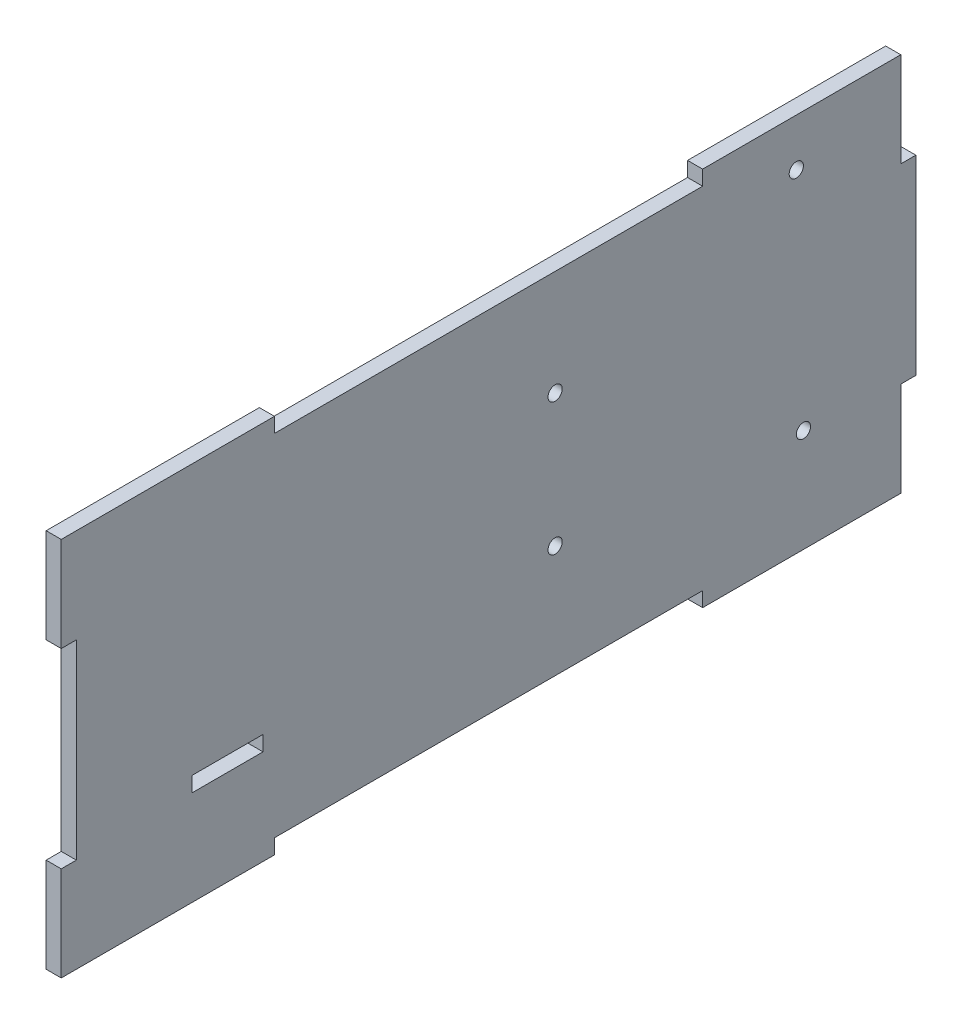
SolidWorks part; units mm, degrees
ref_plane "Front Plane" through (0, 0, 0) normal (0, 0, 1) x (1, 0, 0)
ref_plane "Top Plane" through (0, 0, 0) normal (0, 1, 0) x (1, 0, 0)
ref_plane "Right Plane" through (0, 0, 0) normal (1, 0, 0) x (0, 0, -1)
sketch "Sketch2" plane through (0, 0, 0) normal (1, 0, 0) x (0, 0, -1)
  line L1 (90, -40) -> (-90, -40)
  line L2 (90, -40) -> (90, 40)
  line L3 (90, 40) -> (-90, 40)
  line L4 (-90, -40) -> (-90, 40)
  line L5 (90, -40) -> (-90, 40) construction
  line L6 (90, 40) -> (-90, -40) construction
  point P0 (0, 0)
  dimension "D1" = 180
  dimension "D2" = 80
extrude "Boss-Extrude1" add sketch "Sketch2" along normal blind 3.18
sketch "Sketch3" plane through (3.18, 0, 0) normal (1, 0, 0) x (0, 0, -1)
  line L0 (-90, 40) -> (-90, -40) construction
  line L1 (-90, -20.09) -> (-86.82, -20.09)
  line L2 (-90, -20.09) -> (-90, 20.09)
  line L3 (-90, 20.09) -> (-86.82, 20.09)
  line L4 (-86.82, -20.09) -> (-86.82, 20.09)
  line L11 (0, 0) -> (-100.6733, 0) construction
  point P6 (-90, 0)
  dimension "D1" = 3.18
  dimension "D2" = 40.18
extrude "Cut-Extrude1" cut sketch "Sketch3" against normal up to surface (3.18 mm away) up to face at (0, 0, 0)
sketch "Sketch4" plane through (3.18, 0, 0) normal (1, 0, 0) x (0, 0, -1)
  line L0 (90, 40) -> (-90, 40) construction
  line L1 (-45.09, 40) -> (45.09, 40)
  line L2 (-45.09, 40) -> (-45.09, 36.88)
  line L3 (-45.09, 36.88) -> (45.09, 36.88)
  line L4 (45.09, 40) -> (45.09, 36.88)
  line L7 (0, 0) -> (0, 98.844) construction
  point P13 (0, 40)
  dimension "D1" = 3.12
  dimension "D2" = 90.18
extrude "Cut-Extrude2" cut sketch "Sketch4" against normal up to surface (3.18 mm away) up to face at (0, 0, 44.205)
mirror "Mirror1" about plane through (0, 0, 0) normal (0, 1, 0) of "Cut-Extrude2"
sketch "Sketch5" plane through (3.18, 0, 0) normal (1, 0, 0) x (0, 0, -1)
  line L1 (90, 40) -> (86.82, 40)
  line L2 (90, 40) -> (90, 20.09)
  line L3 (90, 20.09) -> (86.82, 20.09)
  line L4 (86.82, 40) -> (86.82, 20.09)
  line L5 (45.09, -40) -> (90, -40) construction
  dimension "D1" = 3.18
  dimension "D3" = 60.09
  dimension "D2" = 19.91
extrude "Cut-Extrude3" cut sketch "Sketch5" against normal up to surface (3.18 mm away) up to face at (0, 0, 22.1025)
mirror "Mirror2" about plane through (0, 0, 0) normal (0, 1, 0) of "Cut-Extrude3"
sketch "Sketch7" plane through (3.18, 0, 0) normal (1, 0, 0) x (0, 0, -1)
  line L0 (66.32, 30) -> (66.32, -16.8) construction
  line L1 (86.82, 20.09) -> (86.82, 40) construction
  line L2 (14.02, 14.7) -> (14.02, -13.2) construction
  line L3 (86.82, 40) -> (45.09, 40) construction
  line L5 (45.09, 36.88) -> (-45.09, 36.88) construction
  circle A0 centre (64.82, 30) radius 1.5
  circle A1 centre (14.02, 14.7) radius 1.5
  circle A2 centre (14.02, -13.2) radius 1.5
  circle A3 centre (66.32, -18.3) radius 1.5
  dimension "D1" = 50.8
  dimension "D2" = 27.9
  dimension "D3" = 3
  dimension "D4" = 5.1
  dimension "D5" = 48.3
  dimension "D6" = 3
  dimension "D7" = 3
  dimension "D8" = 3
  dimension "D11" = 22.18
  dimension "D9" = 22
  dimension "D10" = 10
extrude "Cut-Extrude4" cut sketch "Sketch7" against normal up to surface (3.18 mm away) up to face at (0, 0, 0.318)
sketch "Sketch8" [suppressed] plane through (0, 0, 0) normal (-1, 0, 0) x (0, 0, 1)
  line L0 (-45.09, -40) -> (-86.82, -40) construction
  line L1 (-62.5, -16.82) -> (-47.5, -16.82)
  line L2 (-62.5, -16.82) -> (-62.5, -20)
  line L3 (-62.5, -20) -> (-47.5, -20)
  line L4 (-47.5, -16.82) -> (-47.5, -20)
  line L5 (-90, -20.09) -> (-90, 20.09) construction
  dimension "D1" = 15
  dimension "D2" = 3.18
  dimension "D3" = 20
  dimension "D4" = 27.5
extrude "Cut-Extrude5" [suppressed] cut sketch "Sketch8" against normal through all
sketch "Sketch9" plane through (0, 0, 0) normal (-1, 0, 0) x (0, 0, 1)
  line L0 (90, -20.09) -> (90, -40) construction
  line L1 (62.5, -16.82) -> (47.5, -16.82)
  line L2 (62.5, -16.82) -> (62.5, -20)
  line L3 (62.5, -20) -> (47.5, -20)
  line L4 (47.5, -16.82) -> (47.5, -20)
  line L5 (90, -40) -> (45.09, -40) construction
  dimension "D1" = 3.18
  dimension "D2" = 15
  dimension "D3" = 27.5
  dimension "D4" = 20
extrude "Cut-Extrude6" cut sketch "Sketch9" against normal through all
equation "\"h\"= 80"
equation "\"w\"= 100"
equation "\"l\"= 180"
equation "\"kerf\"= .18"
equation "\"tablen\"= \"h\" / 2"
equation "\"D1@Sketch2\"=\"l\""
equation "\"D2@Sketch2\"=\"h\""
equation "\"D2@Sketch3\"=40+\"kerf\""
equation "\"D2@Sketch4\"=90+\"kerf\""
equation "\"D2@Sketch5\"=20-\"kerf\"/2"
